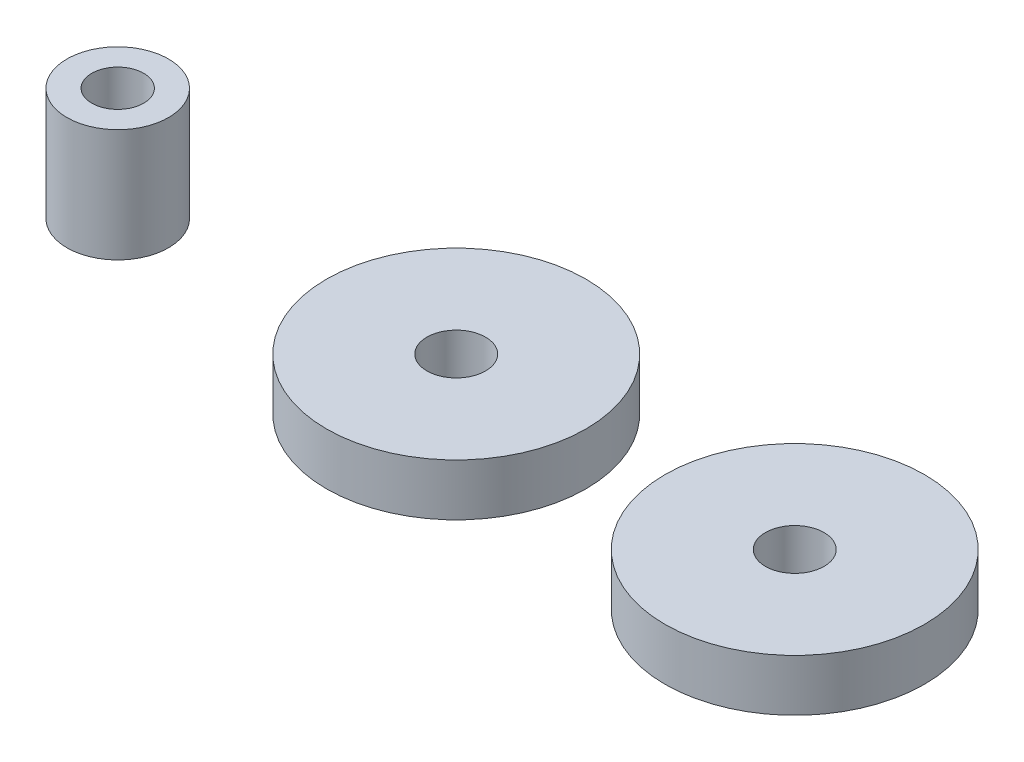
SolidWorks part; units mm, degrees
ref_plane "Front Plane" through (0, 0, 0) normal (0, 0, 1) x (1, 0, 0)
ref_plane "Top Plane" through (0, 0, 0) normal (0, 1, 0) x (1, 0, 0)
ref_plane "Right Plane" through (0, 0, 0) normal (1, 0, 0) x (0, 0, -1)
sketch "Sketch1" plane through (0, 0, 0) normal (0, 1, 0) x (1, 0, 0)
  circle A0 centre (0, 0) radius 1.15
  circle A1 centre (0, 0) radius 2.25
  dimension "D1" = 4.5
  dimension "D2" = 2.3
extrude "Boss-Extrude1" add sketch "Sketch1" along normal blind 5
sketch "Sketch2" plane through (0, 0, 0) normal (0, 1, 0) x (1, 0, 0)
  line L0 (0, 0) -> (15, 0) construction
  line L1 (15, 0) -> (30, 0) construction
  circle A0 centre (15, 0) radius 1.3
  circle A1 centre (15, 0) radius 5.75
  circle A2 centre (30, 0) radius 1.3
  circle A3 centre (30, 0) radius 5.75
  dimension "D1" = 11.5
  dimension "D3" = 2.6
  dimension "D4" = 11.5
  dimension "D6" = 2.6
  dimension "D2" = 15
  dimension "D5" = 15
extrude "Boss-Extrude2" add sketch "Sketch2" along normal blind 2.3 separate body
